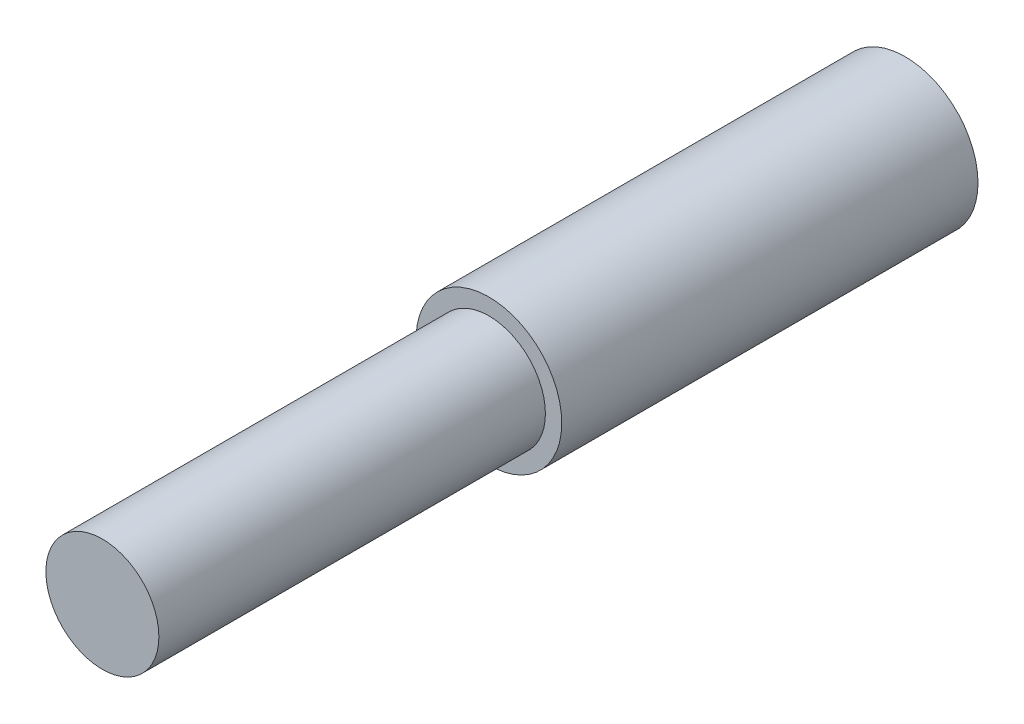
SolidWorks part; units mm, degrees
material "AISI 1020"
ref_plane "Front Plane" through (0, 0, 0) normal (0, 0, 1) x (1, 0, 0)
ref_plane "Top Plane" through (0, 0, 0) normal (0, 1, 0) x (1, 0, 0)
ref_plane "Right Plane" through (0, 0, 0) normal (1, 0, 0) x (0, 0, -1)
sketch "Sketch1" plane through (0, 0, 0) normal (0, 0, 1) x (1, 0, 0)
  circle A0 centre (0, 0) radius 6.223
  dimension "D1" = 12.446
extrude "Boss-Extrude1" add sketch "Sketch1" along normal blind 35.56
sketch "Sketch2" plane through (0, 0, 35.56) normal (0, 0, 1) x (1, 0, 0)
  circle A0 centre (0, 0) radius 4.826
  dimension "D1" = 9.652
extrude "Boss-Extrude2" add sketch "Sketch2" along normal blind 33.02
